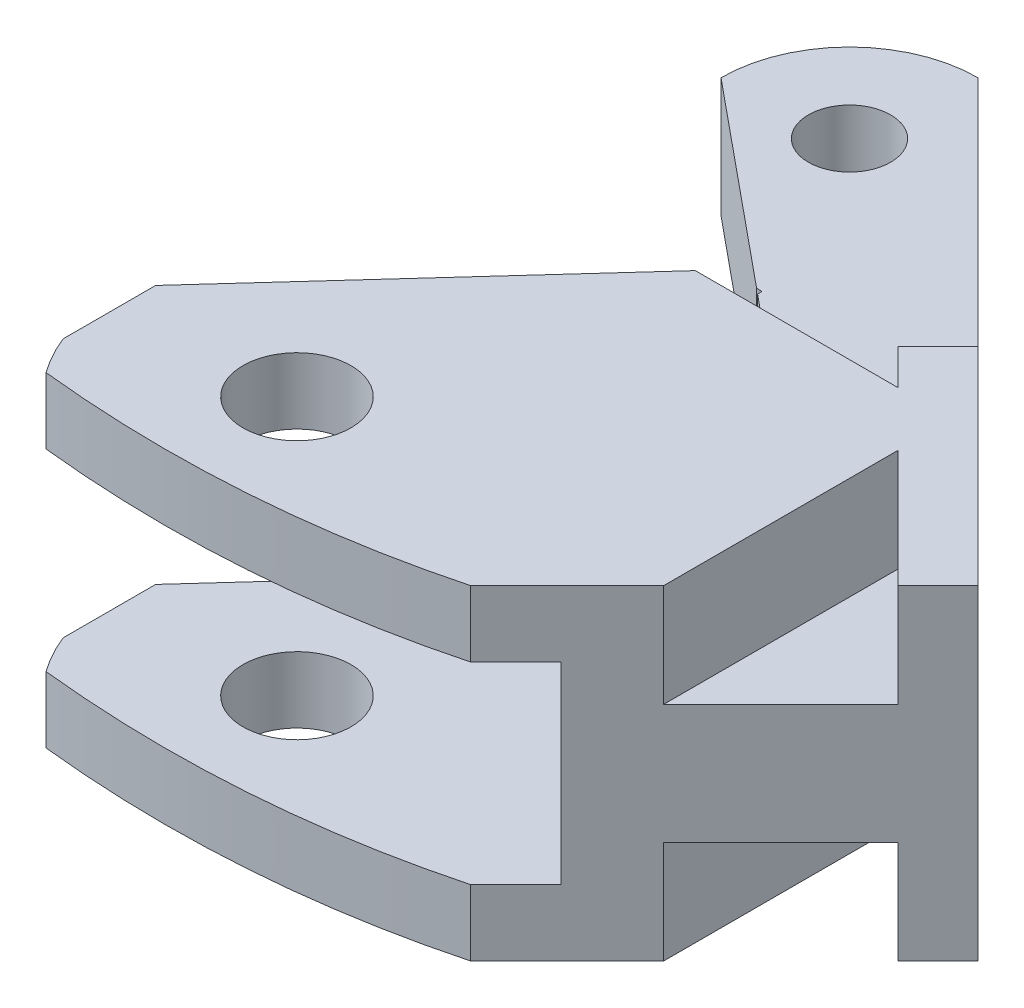
SolidWorks part; units mm, degrees
ref_plane "前视基准面" through (0, 0, 0) normal (0, 0, 1) x (1, 0, 0)
ref_plane "上视基准面" through (0, 0, 0) normal (0, 1, 0) x (1, 0, 0)
ref_plane "右视基准面" through (0, 0, 0) normal (1, 0, 0) x (0, 0, -1)
sketch "草图1" plane through (0, 0, 0) normal (0, 1, 0) x (1, 0, 0)
  line L0 (5, 0) -> (20, 0)
  line L1 (9, -16) -> (20, -16)
  line L3 (9, -16) -> (9, -35)
  line L4 (0, -35) -> (9, -35)
  line L5 (0, -27) -> (0, -5)
  line L6 (0, -27) -> (0, -35)
  line L7 (20, -16) -> (20, 0)
  circle A0 centre (4.55, -4.55) radius 1.6
  arc A1 (5, 0) -> (0, -5) centre (5, -5) ccw
  point P11 (0, 0)
extrude "凸台-拉伸1" add sketch "草图1" along normal blind 4.65
sketch "草图7" plane through (0, 4.65, 0) normal (0, 1, 0) x (1, 0, 0)
  line L0 (9, -35) -> (9, -16) construction
  line L1 (0, -35) -> (9, -35)
  line L2 (0, -35) -> (0, -16)
  line L3 (0, -16) -> (9, -16)
  line L4 (9, -35) -> (9, -16)
extrude "凸台-拉伸4" add sketch "草图7" along normal blind 4
sketch "草图8" plane through (0, 0, 0) normal (0, -1, 0) x (1, 0, 0)
  line L0 (0, 5) -> (0, 35) construction
  line L1 (0, 35) -> (9, 35)
  line L2 (0, 35) -> (0, 16)
  line L3 (0, 16) -> (9, 16)
  line L4 (9, 35) -> (9, 16)
  line L5 (9, 35) -> (9, 16) construction
extrude "凸台-拉伸5" add sketch "草图8" along normal blind 4
sketch "草图9" plane through (0, 0, 0) normal (-1, 0, 0) x (0, 0, 1)
  line L0 (35, 8.65) -> (35, -4) construction
  line L1 (35, 6.075) -> (19, 6.075)
  line L2 (35, 6.075) -> (35, -1.425)
  line L3 (35, -1.425) -> (19, -1.425)
  line L4 (19, 6.075) -> (19, -1.425)
extrude "切除-拉伸3" cut sketch "草图9" against normal blind 9
sketch "草图11" plane through (0, 8.65, 0) normal (0, 1, 0) x (1, 0, 0)
  circle A1 centre (6.5, -28) radius 2.1
extrude "切除-拉伸5" cut sketch "草图11" against normal blind 26.4
sketch "草图12" plane through (9, 0, 0) normal (1, 0, 0) x (0, 0, -1)
  line L0 (-35, 8.65) -> (-35, 6.075)
  line L1 (-35, 6.075) -> (-19, 6.075)
  line L2 (-19, 6.075) -> (-19, -1.425)
  line L3 (-19, -1.425) -> (-35, -1.425)
  line L4 (-35, -1.425) -> (-35, -4)
  line L5 (-35, -4) -> (-16, -4)
  line L6 (-16, -4) -> (-16, 8.65)
  line L7 (-16, 8.65) -> (-35, 8.65)
extrude "凸台-拉伸6" add sketch "草图12" along normal blind 9
sketch "草图13" plane through (18, 0, 0) normal (1, 0, 0) x (0, 0, -1)
  line L0 (-35, 8.65) -> (-35, -4)
  line L1 (-35, -4) -> (-16, -4)
  line L2 (-16, -4) -> (-16, 8.65)
  line L3 (-16, 8.65) -> (-35, 8.65)
extrude "凸台-拉伸7" add sketch "草图13" along normal blind 2
sketch "草图15" plane through (0, 0, 0) normal (-1, 0, 0) x (0, 0, 1)
  line L2 (19, -1.425) -> (11.4034, -1.425)
  line L3 (19, -1.425) -> (19, 6.075)
  line L4 (19, 6.075) -> (11.4034, 6.075)
  line L7 (11.4034, -1.425) -> (11.4034, 6.075)
extrude "切除-拉伸6" cut sketch "草图15" against normal blind 8
sketch "草图16" plane through (0, 4.65, 0) normal (0, 1, 0) x (1, 0, 0)
  line L0 (0, -5) -> (5.8909, -11.4034)
  line L1 (8, -11.4034) -> (0, -11.4034) construction
  line L2 (5.8909, -11.4034) -> (0, -11.4034)
  line L3 (0, -11.4034) -> (0, -5)
extrude "切除-拉伸7" cut sketch "草图16" against normal blind 8
sketch "草图17" plane through (0, 0, 0) normal (0, -1, 0) x (1, 0, 0)
  line L1 (20, 35) -> (20, 15)
  line L3 (31.0646, 26.0646) -> (20, 15)
  arc A0 (20, 35) -> (31.0646, 26.0646) centre (4.55, 4.55) cw
extrude "凸台-拉伸8" add sketch "草图17" against normal blind 4.65
sketch "草图19" plane through (0, 4.65, 0) normal (0, 1, 0) x (1, 0, 0)
  line L0 (20, -15) -> (5, 0)
  line L1 (5, 0) -> (20, 0)
  line L2 (20, 0) -> (20, -15)
extrude "切除-拉伸9" cut sketch "草图19" against normal blind 4.65
sketch "草图20" plane through (0, -1.425, 0) normal (0, 1, 0) x (1, 0, 0)
  line L0 (8, -19) -> (8, -16)
  line L1 (8, -16) -> (13.3802, -16)
  line L2 (13.3802, -16) -> (13.3802, -19)
  line L3 (18, -19) -> (8, -19) construction
  line L4 (13.3802, -19) -> (8, -19)
extrude "切除-拉伸10" cut sketch "草图20" along normal blind 7.5
sketch "草图21" plane through (0, 0, 0) normal (0, -1, 0) x (1, 0, 0)
  line L0 (13.3802, 16) -> (0, 5)
  line L1 (0, 5) -> (8, 16)
  line L2 (8, 11.4034) -> (8, 16) construction
  line L3 (8, 16) -> (13.3802, 16) construction
  line L4 (8, 16) -> (13.3802, 16)
  arc A0 (0, 5) -> (5, 0) centre (5, 5) ccw construction
extrude "切除-拉伸11" cut sketch "草图21" against normal blind 4.65
sketch "草图22" plane through (0, 8.65, 0) normal (0, 1, 0) x (1, 0, 0)
  line L0 (0, -16) -> (10, -16)
  line L1 (20, -16) -> (0, -16) construction
  line L2 (10, -16) -> (0, -27)
  line L3 (0, -16) -> (0, -35) construction
  line L4 (0, -27) -> (0, -16)
extrude "切除-拉伸13" cut sketch "草图22" against normal blind 13
sketch "草图23" plane through (0, 8.65, 0) normal (0, 1, 0) x (1, 0, 0)
  line L0 (6.5, -35) -> (0, -35)
  line L1 (0, -35) -> (0, -30.5981)
  line L2 (0, -27) -> (0, -35) construction
  arc A0 (0, -30.5981) -> (6.5, -35) centre (6.5, -28) ccw
extrude "切除-拉伸15" cut sketch "草图23" against normal blind 13
sketch "草图26" plane through (2.5, 0, -2.5) normal (0.7071, 0, -0.7071) x (-0.7071, 0, -0.7071)
  line L1 (-40.3965, 8.65) -> (-22, 8.65)
  line L2 (-40.3965, 8.65) -> (-40.3965, -4)
  line L3 (-40.3965, -4) -> (-22, -4)
  line L4 (-22, 8.65) -> (-22, -4)
extrude "凸台-拉伸9" add sketch "草图26" against normal blind 2.2
sketch "草图28" plane through (2.5, 0, -2.5) normal (0.7071, 0, -0.7071) x (-0.7071, 0, -0.7071)
  line L0 (-22, 8.65) -> (-40.3965, 8.65) construction
  line L1 (-40.8965, -4) -> (-38.3965, -4)
  line L2 (-40.8965, -4) -> (-40.8965, 8.65)
  line L3 (-40.8965, 8.65) -> (-38.3965, 8.65)
  line L4 (-38.3965, -4) -> (-38.3965, 8.65)
extrude "切除-拉伸17" cut sketch "草图28" against normal blind 18
sketch "草图29" plane through (0, -4, 0) normal (0, -1, 0) x (1, 0, 0)
  line L0 (29.6504, 24.6504) -> (19.3008, 35)
  line L1 (19.3008, 35) -> (1.7736, 35)
  line L2 (1.7736, 35) -> (0.8039, 32.0688)
  arc A1 (6.5, 35) -> (0, 30.5981) centre (6.5, 28) ccw construction
  spline S0 degree 2 poles (29.6504, 24.6504) (16.7115, 33.7569) (0.8039, 32.0688) knots 0 0 0 1 1 1
extrude "切除-拉伸18" cut sketch "草图29" against normal blind 14
sketch "草图31" plane through (2.5, 0, -2.5) normal (0.7071, 0, -0.7071) x (-0.7071, 0, -0.7071)
  line L0 (-38.3965, -4) -> (-22, -4) construction
  line L1 (-38.3965, 8.65) -> (-33.3965, 8.65)
  line L2 (-38.3965, 8.65) -> (-38.3965, -4)
  line L3 (-38.3965, -4) -> (-33.3965, -4)
  line L4 (-33.3965, 8.65) -> (-33.3965, -4)
extrude "切除-拉伸19" cut sketch "草图31" against normal blind 20
